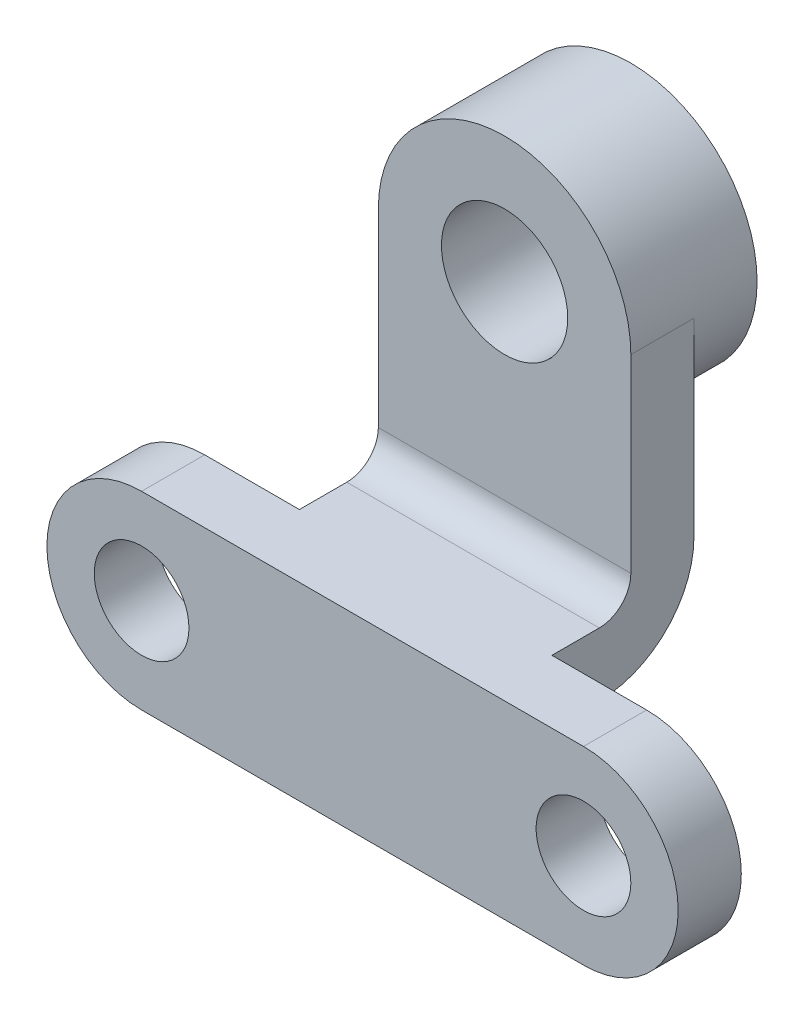
SolidWorks part; units mm, degrees
ref_plane "Front Plane" through (0, 0, 0) normal (0, 0, 1) x (1, 0, 0)
ref_plane "Top Plane" through (0, 0, 0) normal (0, 1, 0) x (1, 0, 0)
ref_plane "Right Plane" through (0, 0, 0) normal (1, 0, 0) x (0, 0, -1)
sketch "Sketch1" plane through (0, 0, 0) normal (0, 0, 1) x (1, 0, 0)
  line L0 (-88.9, 0) -> (88.9, 0) construction
  line L1 (-88.9, 38.1) -> (88.9, 38.1)
  line L2 (-88.9, -38.1) -> (88.9, -38.1)
  arc A0 (-88.9, 38.1) -> (-88.9, -38.1) centre (-88.9, 0) ccw
  arc A1 (88.9, -38.1) -> (88.9, 38.1) centre (88.9, 0) ccw
  circle A2 centre (-88.9, 0) radius 19.05
  circle A3 centre (88.9, 0) radius 19.05
  point P2 (0, 0)
  point P12 (0, 0)
  point P13 (0, 0)
  dimension "D1" = 38.1
  dimension "D3" = 38.1
  dimension "D4" = 38.1
  dimension "D2" = 177.8
extrude "Boss-Extrude1" add sketch "Sketch1" against normal blind 25.4
sketch "Sketch2" plane through (0, 0, -25.4) normal (0, 0, -1) x (-1, 0, 0)
  line L0 (-88.9, 38.1) -> (88.9, 38.1) construction
  line L1 (-50.8, 38.1) -> (50.8, 38.1)
  line L2 (-50.8, 38.1) -> (-50.8, 12.7)
  line L3 (-50.8, 12.7) -> (50.8, 12.7)
  line L4 (50.8, 38.1) -> (50.8, 12.7)
  circle A0 centre (88.9, 0) radius 19.05 construction
  dimension "D1" = 25.4
  dimension "D2" = 101.6
  dimension "D3" = 38.1
extrude "Boss-Extrude2" add sketch "Sketch2" along normal blind 57.15 contours L2 L1 L4 L3
sketch "Sketch5" plane through (0, 38.1, 0) normal (0, 1, 0) x (1, 0, 0)
  line L0 (50.8, 82.55) -> (50.8, 25.4) construction
  line L1 (-50.8, 82.55) -> (50.8, 82.55)
  line L2 (-50.8, 82.55) -> (-50.8, 57.15)
  line L3 (-50.8, 57.15) -> (50.8, 57.15)
  line L4 (50.8, 82.55) -> (50.8, 57.15)
  dimension "D1" = 25.4
extrude "Boss-Extrude3" add sketch "Sketch5" along normal blind 88.9
sketch "Sketch6" plane through (0, 0, -57.15) normal (0, 0, 1) x (1, 0, 0)
  line L0 (-50.8, 127) -> (50.8, 127) construction
  circle A0 centre (0, 127) radius 50.8
extrude "Boss-Extrude4" add sketch "Sketch6" against normal blind 50.8
sketch "Sketch7" plane through (0, 0, -57.15) normal (0, 0, 1) x (1, 0, 0)
  circle A0 centre (0, 127) radius 25.4
extrude "Cut-Extrude1" cut sketch "Sketch7" against normal blind 50.8
fillet "Fillet1" radius 12.7 1 edges at (0, 38.1, -57.15)
fillet "Fillet2" radius 38.1 1 edges at (0, 12.7, -82.55)
equation "\"cirlce\"=1.5"
equation "\"D3@Sketch1\"=\"cirlce\""
